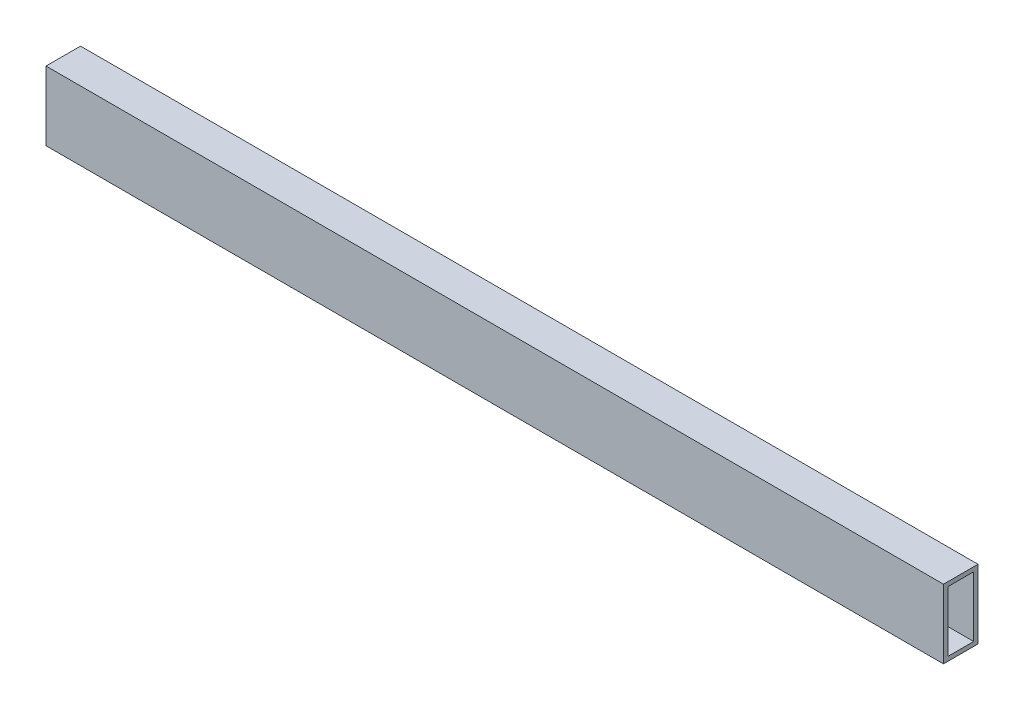
SolidWorks part; units mm, degrees
material "6061 Alloy"
ref_plane "Front Plane" through (0, 0, 0) normal (0, 0, 1) x (1, 0, 0)
ref_plane "Top Plane" through (0, 0, 0) normal (0, 1, 0) x (1, 0, 0)
ref_plane "Right Plane" through (0, 0, 0) normal (1, 0, 0) x (0, 0, -1)
sketch "Sketch1" plane through (0, 0, 0) normal (0, 1, 0) x (1, 0, 0)
  line L1 (-330.2, 12.7) -> (330.2, 12.7)
  line L2 (-330.2, 12.7) -> (-330.2, -12.7)
  line L3 (-330.2, -12.7) -> (330.2, -12.7)
  line L4 (330.2, 12.7) -> (330.2, -12.7)
  line L5 (-330.2, 12.7) -> (330.2, -12.7) construction
  line L6 (-330.2, -12.7) -> (330.2, 12.7) construction
  point P0 (0, 0)
  dimension "D1" = 660.4
  dimension "D2" = 25.4
extrude "Boss-Extrude1" add sketch "Sketch1" along normal mid plane 50.8
shell "Shell1" thickness 3.175
sketch "Sketch2" plane through (0, 25.4, 0) normal (0, 1, 0) x (1, 0, 0)
  line L0 (330.2, -12.7) -> (330.2, 12.7) construction
  line L1 (330.2, 12.7) -> (-330.2, 12.7) construction
  circle A0 centre (317.5, 0) radius 3.175
  circle A1 centre (292.1, 0) radius 3.175
  circle A2 centre (266.7, 0) radius 3.175
  circle A3 centre (241.3, 0) radius 3.175
  circle A4 centre (215.9, 0) radius 3.175
  circle A5 centre (190.5, 0) radius 3.175
  circle A6 centre (165.1, 0) radius 3.175
  circle A7 centre (139.7, 0) radius 3.175
  circle A8 centre (114.3, 0) radius 3.175
  circle A9 centre (88.9, 0) radius 3.175
  circle A10 centre (63.5, 0) radius 3.175
  circle A11 centre (38.1, 0) radius 3.175
  circle A12 centre (12.7, 0) radius 3.175
  circle A13 centre (-12.7, 0) radius 3.175
  circle A14 centre (-38.1, 0) radius 3.175
  circle A15 centre (-63.5, 0) radius 3.175
  circle A16 centre (-88.9, 0) radius 3.175
  circle A17 centre (-114.3, 0) radius 3.175
  circle A18 centre (-139.7, 0) radius 3.175
  circle A19 centre (-165.1, 0) radius 3.175
  circle A20 centre (-190.5, 0) radius 3.175
  circle A21 centre (-215.9, 0) radius 3.175
  circle A22 centre (-241.3, 0) radius 3.175
  circle A23 centre (-266.7, 0) radius 3.175
  circle A24 centre (-292.1, 0) radius 3.175
  circle A25 centre (-317.5, 0) radius 3.175
  circle A26 centre (-342.9, 0) radius 3.175
  circle A27 centre (-368.3, 0) radius 3.175
  circle A28 centre (-393.7, 0) radius 3.175
  circle A29 centre (-419.1, 0) radius 3.175
  circle A30 centre (-444.5, 0) radius 3.175
  circle A31 centre (-469.9, 0) radius 3.175
  circle A32 centre (-495.3, 0) radius 3.175
  circle A33 centre (-520.7, 0) radius 3.175
  circle A34 centre (-546.1, 0) radius 3.175
  circle A35 centre (-571.5, 0) radius 3.175
  circle A36 centre (-596.9, 0) radius 3.175
  circle A37 centre (-622.3, 0) radius 3.175
  circle A38 centre (-647.7, 0) radius 3.175
  circle A39 centre (-673.1, 0) radius 3.175
  circle A40 centre (-698.5, 0) radius 3.175
  circle A41 centre (-723.9, 0) radius 3.175
  circle A42 centre (-749.3, 0) radius 3.175
  circle A43 centre (-774.7, 0) radius 3.175
  circle A44 centre (-800.1, 0) radius 3.175
  circle A45 centre (-825.5, 0) radius 3.175
  circle A46 centre (-850.9, 0) radius 3.175
  circle A47 centre (-876.3, 0) radius 3.175
  circle A48 centre (-901.7, 0) radius 3.175
  circle A49 centre (-927.1, 0) radius 3.175
  circle A50 centre (-952.5, 0) radius 3.175
  circle A51 centre (-977.9, 0) radius 3.175
  circle A52 centre (-1003.3, 0) radius 3.175
  circle A53 centre (-1028.7, 0) radius 3.175
  circle A54 centre (-1054.1, 0) radius 3.175
  circle A55 centre (-1079.5, 0) radius 3.175
  circle A56 centre (-1104.9, 0) radius 3.175
  circle A57 centre (-1130.3, 0) radius 3.175
  circle A58 centre (-1155.7, 0) radius 3.175
  circle A59 centre (-1181.1, 0) radius 3.175
  dimension "D1" = 6.35
  dimension "D2" = 12.7
  dimension "D3" = 12.7
  dimension "D5" = 25.4
  dimension "D4" = 60
extrude "Cut-Extrude1" [suppressed] cut sketch "Sketch2" against normal through all
equation "\"A\"= 1"
equation "\"B\"= 2'\""
equation "\"C\"= 26"
equation "\"D\"= 1 / 8"
equation "\"D1@Sketch1\"=\"C\""
equation "\"D2@Sketch1\"=\"A\""
equation "\"D1@Boss-Extrude1\"=\"B\""
equation "\"D1@Shell1\"=\"D\""
